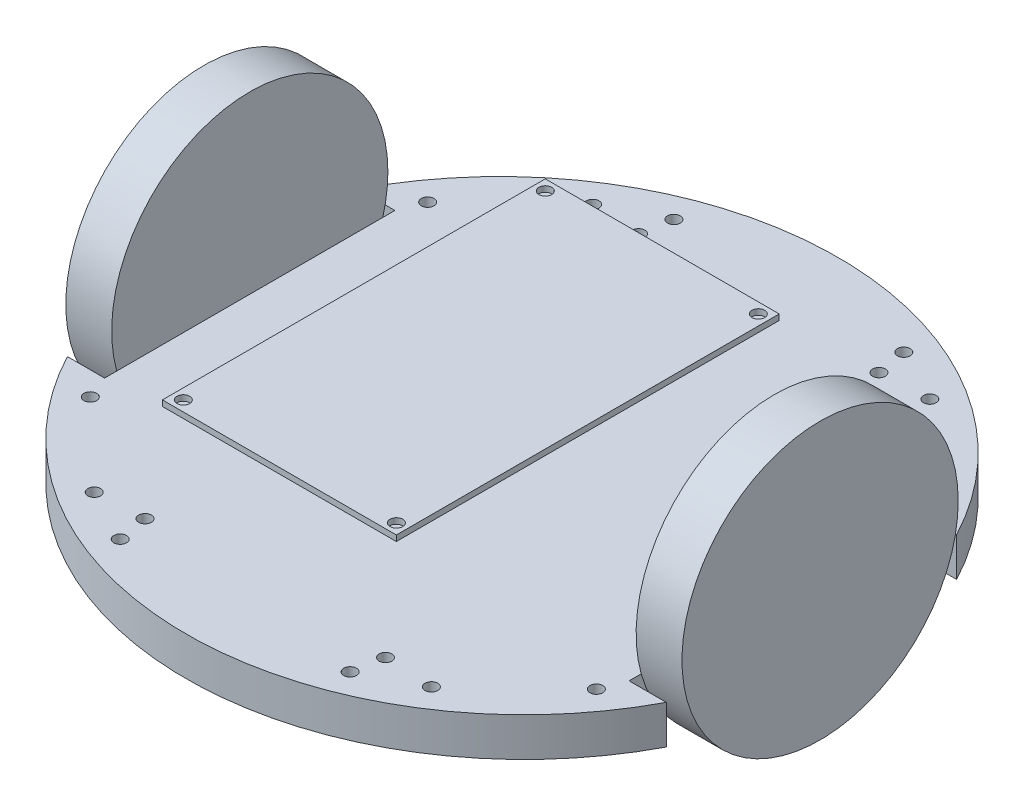
SolidWorks part; units mm, degrees
ref_plane "Front Plane" through (0, 0, 0) normal (0, 0, 1) x (1, 0, 0)
ref_plane "Top Plane" through (0, 0, 0) normal (0, 1, 0) x (1, 0, 0)
ref_plane "Right Plane" through (0, 0, 0) normal (1, 0, 0) x (0, 0, -1)
sketch "Sketch2" plane through (0, 0, 0) normal (0, 1, 0) x (1, 0, 0)
  line L0 (74.6125, 72.3392) -> (74.6125, 117.4242)
  line L1 (0, 72.3392) -> (149.225, 72.3392)
  line L2 (0, 72.3392) -> (0, 0)
  line L3 (0, 0) -> (149.225, 0)
  line L4 (149.225, 72.3392) -> (149.225, 0)
  line L6 (0, 72.3392) -> (9.271, 72.3392)
  line L7 (0, 72.3392) -> (0, 0)
  line L8 (0, 0) -> (9.271, 0)
  line L9 (9.271, 72.3392) -> (9.271, 0)
  line L10 (149.225, 72.3392) -> (139.954, 72.3392)
  line L11 (149.225, 72.3392) -> (149.225, 0)
  line L12 (149.225, 0) -> (139.954, 0)
  line L13 (139.954, 72.3392) -> (139.954, 0)
  arc A1 (0, 72.3392) -> (149.225, 72.3392) centre (74.6125, 33.1425) cw
  dimension "D1" = 149.225
  dimension "D3" = 0
  dimension "D5" = 9.271
  dimension "D2" = 72.3392
  dimension "D4" = 45.085
  dimension "D6" = 9.271
extrude "Boss-Extrude1" add sketch "Sketch2" along normal blind 9.652 contours A1 L1 L0 | A1 L0 L1 | L13 L1 L9 L3
sketch "Sketch4" plane through (0, 0, 0) normal (0, -1, 0) x (1, 0, 0)
  line L0 (139.954, -72.3392) -> (149.225, -72.3392) construction
  line L2 (139.954, -72.3392) -> (139.954, 0) construction
  line L3 (0, -72.3392) -> (9.271, -72.3392) construction
  circle A2 centre (116.6197, -98.2703) radius 1.5875
  arc A3 (7.7555, -72.3392) -> (141.4695, -72.3392) centre (74.6125, -33.1425) ccw
  arc A4 (0, -72.3392) -> (149.225, -72.3392) centre (74.6125, -33.1425) ccw construction
  circle A5 centre (137.668, -78.2007) radius 1.5875
  circle A6 centre (103.2523, -105.1564) radius 1.5875
  circle A7 centre (104.5706, -97.6513) radius 1.5875
  dimension "D1" = 3.175
  dimension "D3" = 29.083
  dimension "D4" = 0
  dimension "D5" = 0
  dimension "D6" = 6.7818
  dimension "D7" = 3.175
  dimension "D2" = 2.286
  dimension "D8" = 3.175
  dimension "D9" = 15.0368
  dimension "D10" = 3.175
  dimension "D11" = 12.065
  dimension "D12" = 7.62
extrude "Cut-Extrude1" cut sketch "Sketch4" against normal blind 9.652 contours A7 | A6 | A2 | A5
sketch "Sketch5" plane through (0, 0, 0) normal (0, -1, 0) x (1, 0, 0)
  line L0 (74.6125, 0) -> (74.6125, -117.4242)
  line L1 (9.271, 0) -> (139.954, 0) construction
  line L2 (9.271, -36.1696) -> (139.954, -36.1696)
  line L3 (9.271, -72.3392) -> (9.271, 0) construction
  line L4 (139.954, -72.3392) -> (139.954, 0) construction
  arc A0 (0, -72.3392) -> (149.225, -72.3392) centre (74.6125, -33.1425) ccw construction
  dimension "D1" = 0
ref_plane "Plane1" through (74.6125, 0, 0) normal (1, 0, 0) x (0, 0, -1)
ref_plane "Plane2" through (0, 0, -36.1696) normal (0, 0, 1) x (1, 0, 0)
mirror "Mirror1" about plane through (0, 0, -36.1696) normal (0, 0, 1) of "Boss-Extrude1"
mirror "Mirror2" about plane through (74.6125, 0, 0) normal (1, 0, 0) of "Cut-Extrude1"
mirror "Mirror3" about plane through (0, 0, -36.1696) normal (0, 0, 1) of "Mirror2", "Cut-Extrude1"
sketch "Sketch6" plane through (139.954, 0, 0) normal (1, 0, 0) x (0, 0, -1)
  line L0 (36.1696, 71.8756) -> (36.1696, -71.8756) construction
  line L2 (72.3392, 0) -> (0, 0) construction
  circle A0 centre (36.1696, 18.923) radius 34.417
  dimension "D1" = 68.834
  dimension "D2" = 0
  dimension "D3" = 18.923
extrude "Boss-Extrude2" add sketch "Sketch6" along normal blind 11.43
ref_plane "Plane3" through (0, 32.512, 0) normal (0, 1, 0) x (1, 0, 0)
sketch "Sketch7" plane through (0, 32.512, 0) normal (0, 1, 0) x (1, 0, 0)
  line L0 (74.6125, -5.3086) -> (74.6125, 5.3086) construction
  line L1 (45.466, 73.6092) -> (103.759, 73.6092)
  line L2 (45.466, 73.6092) -> (45.466, -21.7932)
  line L3 (45.466, -21.7932) -> (103.759, -21.7932)
  line L4 (103.759, 73.6092) -> (103.759, -21.7932)
  line L5 (-71.8756, 36.1696) -> (71.8756, 36.1696) construction
  dimension "D1" = 58.293
  dimension "D2" = 95.4024
  dimension "D3" = 29.1465
  dimension "D4" = 37.4396
extrude "Boss-Extrude3" add sketch "Sketch7" along normal blind 1.4224 separate body
sketch "Sketch8" plane through (0, 33.9344, 0) normal (0, 1, 0) x (1, 0, 0)
  line L0 (45.466, -21.7932) -> (103.759, -21.7932) construction
  line L1 (103.759, -21.7932) -> (103.759, 73.6092) construction
  line L2 (45.466, 73.6092) -> (45.466, -21.7932) construction
  line L3 (103.759, 73.6092) -> (45.466, 73.6092) construction
  circle A0 centre (101.1555, -19.1897) radius 1.5875
  circle A1 centre (48.0695, -19.1897) radius 1.5875
  circle A2 centre (101.1555, 71.0057) radius 1.5875
  circle A3 centre (48.0695, 71.0057) radius 1.5875
  dimension "D1" = 3.175
  dimension "D2" = 3.175
  dimension "D3" = 2.6035
  dimension "D4" = 2.6035
  dimension "D5" = 2.6035
  dimension "D6" = 2.6035
  dimension "D7" = 3.175
  dimension "D8" = 3.175
  dimension "D9" = 2.6035
  dimension "D10" = 2.6035
  dimension "D11" = 2.6035
  dimension "D12" = 2.6035
extrude "Cut-Extrude2" cut sketch "Sketch8" against normal blind 1.4224
mirror "Mirror4" about plane through (74.6125, 0, 0) normal (1, 0, 0) of "Boss-Extrude2"
sketch "Sketch9" plane through (0, 0, 0) normal (0, -1, 0) x (1, 0, 0)
  circle A0 centre (33.867, 22.519) radius 1.5875
  circle A1 centre (47.2344, 29.405) radius 1.5875
  circle A2 centre (104.514, 29.405) radius 1.5875
  circle A3 centre (117.8814, 22.519) radius 1.5875
  dimension "D1" = 3.175
  dimension "D2" = 3.175
  dimension "D3" = 3.175
  dimension "D4" = 3.175
  dimension "D5" = 6.8861
  dimension "D6" = 13.3674
  dimension "D7" = 57.2796
  dimension "D8" = 6.8861
  dimension "D9" = 13.3674
  dimension "D10" = 0
ref_plane "Plane4" through (0, -15.494, 0) normal (0, -1, 0) x (-1, 0, 0)
ref_plane "Plane5" through (74.6125, 0, 0) normal (-1, 0, 0) x (0, 0, 1)
